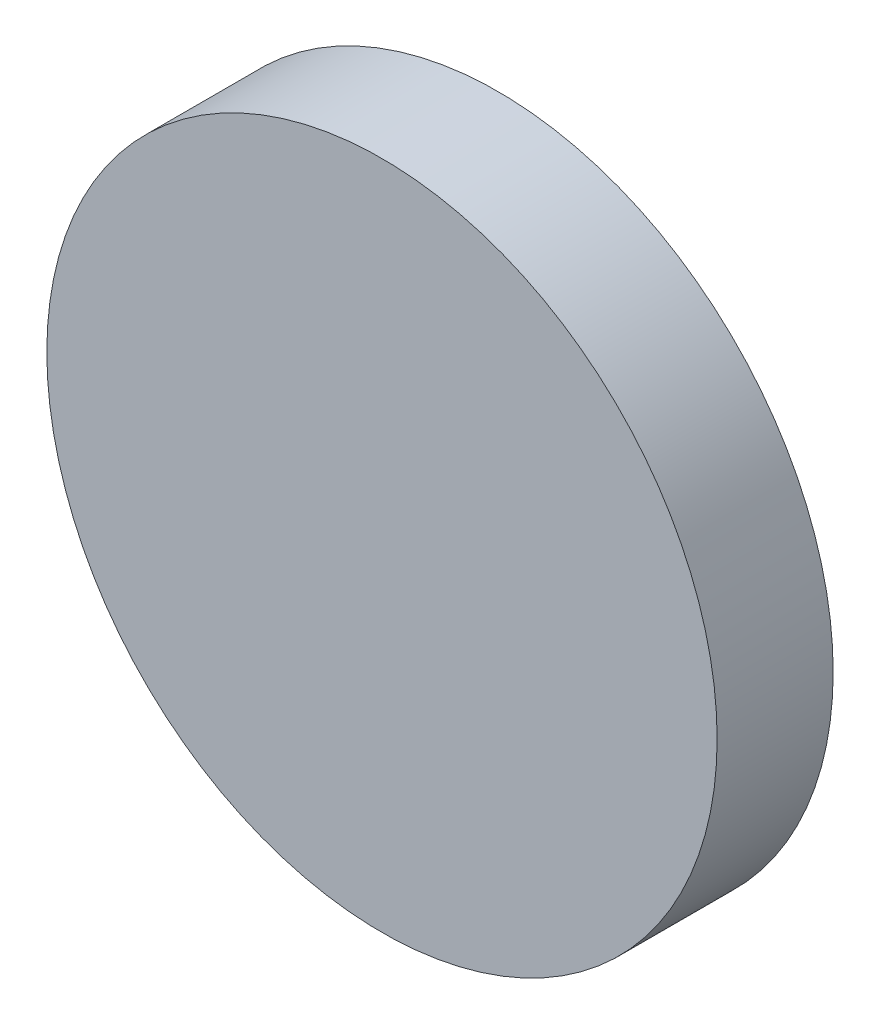
SolidWorks part; units mm, degrees
ref_plane "Front Plane" through (0, 0, 0) normal (0, 0, 1) x (1, 0, 0)
ref_plane "Top Plane" through (0, 0, 0) normal (0, 1, 0) x (1, 0, 0)
ref_plane "Right Plane" through (0, 0, 0) normal (1, 0, 0) x (0, 0, -1)
sketch "Sketch1" plane through (0, 0, 0) normal (0, 0, 1) x (1, 0, 0)
  circle A0 centre (0, 0) radius 65
  dimension "D1" = 130
extrude "Boss-Extrude1" add sketch "Sketch1" along normal blind 22.5 contours A0
